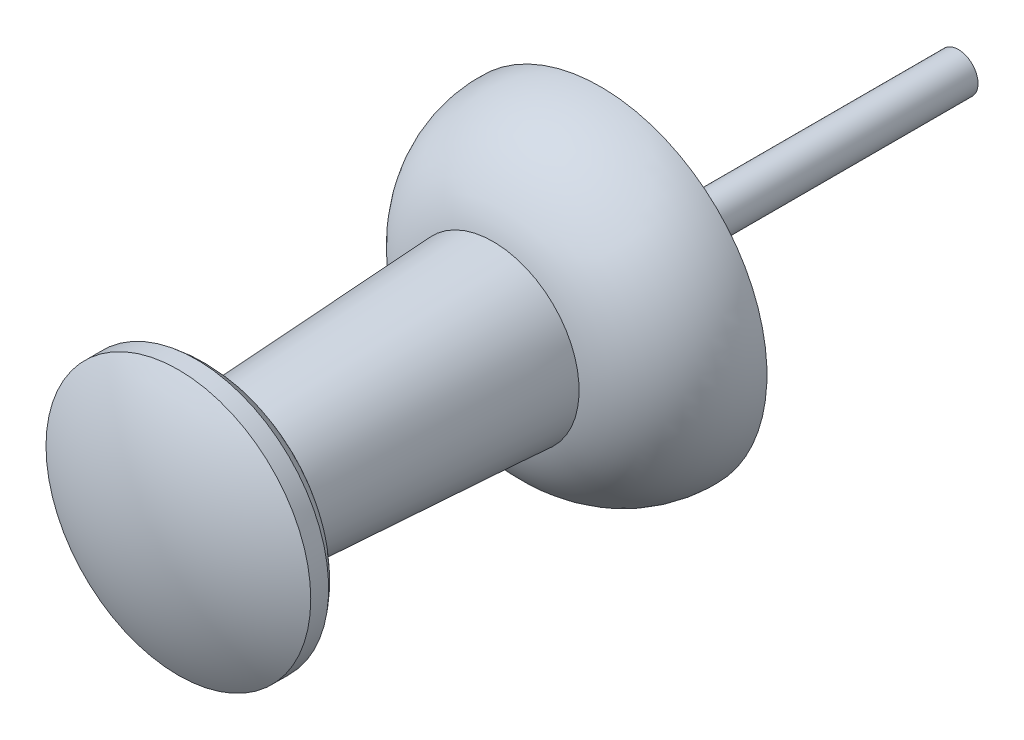
SolidWorks part; units mm, degrees
ref_plane "Front Plane" through (0, 0, 0) normal (0, 0, 1) x (1, 0, 0)
ref_plane "Top Plane" through (0, 0, 0) normal (0, 1, 0) x (1, 0, 0)
ref_plane "Right Plane" through (0, 0, 0) normal (1, 0, 0) x (0, 0, -1)
ref_axis "Axis1" through (0, 0, -88.99) along (0, 0, 1)
sketch "Sketch2" plane through (0, 0, 0) normal (1, 0, 0) x (0, 0, -1)
  line L0 (10, 0.55) -> (0, 0.55)
  line L1 (0, 0) -> (-12.8, 0)
  line L2 (88.99, 0) -> (-88.99, 0) construction
  line L3 (-3, 2.4) -> (-10.5, 2)
  line L4 (-11.8, 3.7) -> (-11.3, 3.7)
  line L5 (0, 0.55) -> (0, 4.65)
  line L6 (10, 0.55) -> (10, 0)
  line L7 (10, 0) -> (0, 0)
  arc A0 (-3, 2.4) -> (0, 4.65) centre (-0.0949, 1.6515) cw
  arc A1 (-10.5, 2) -> (-11.3, 3.7) centre (-12.4976, 2.0982) ccw
  arc A2 (-12.8, 0) -> (-11.8, 3.7) centre (-5.455, 0) cw
  point P11 (0, 0)
  point P15 (0, 0)
  point P16 (0, 0)
  point P17 (-10.688, 2.9498)
  dimension "D5" = 3
  dimension "D9" = 1
  dimension "D10" = 0.5
  dimension "D1" = 4.65
  dimension "D2" = 12.8
  dimension "D3" = 3.7
  dimension "D4" = 2
  dimension "D6" = 2.4
  dimension "D7" = 3
  dimension "D8" = 10.5
  dimension "D11" = 2
  dimension "D12" = 10
  dimension "D13" = 0.55
revolve "Revolve1" add sketch "Sketch2" angle 360 about axis through (0, 0, -88.99) along (0, 0, 1)
